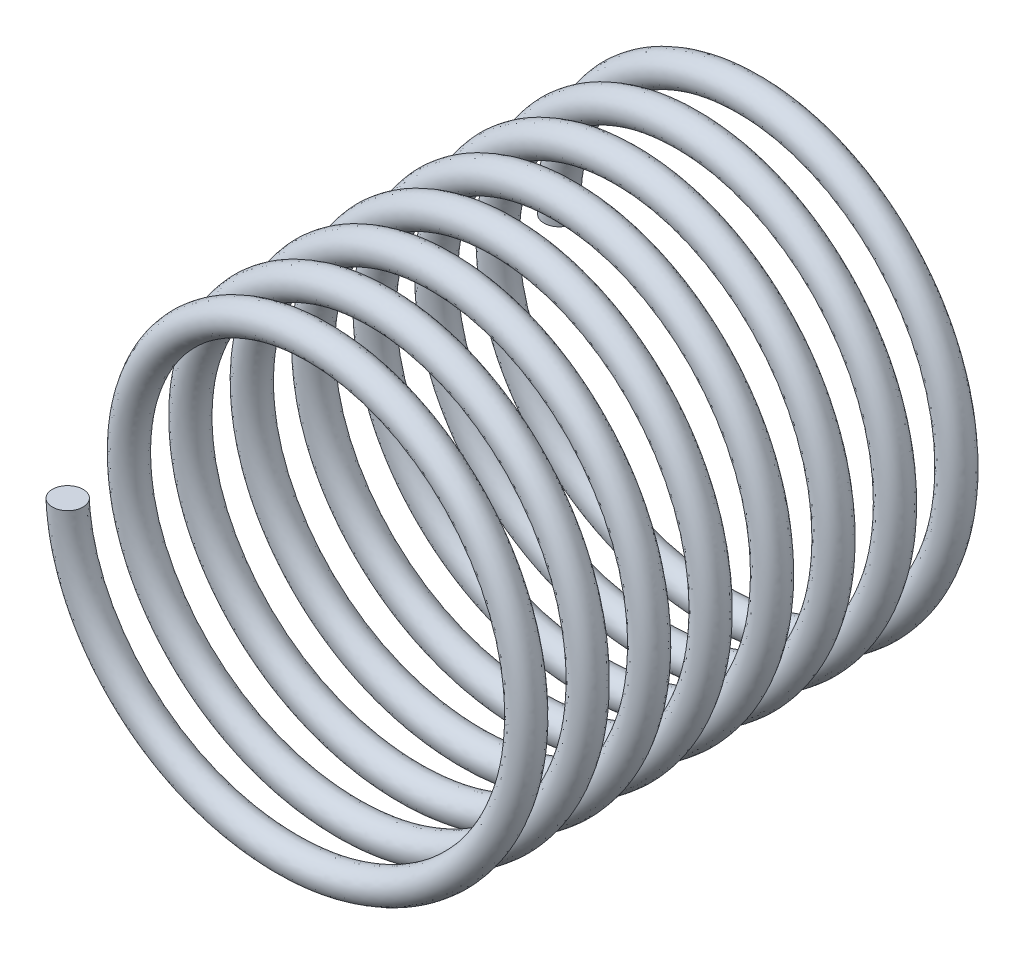
SolidWorks part; units mm, degrees
ref_plane "Front Plane" through (0, 0, 0) normal (0, 0, 1) x (1, 0, 0)
ref_plane "Top Plane" through (0, 0, 0) normal (0, 1, 0) x (1, 0, 0)
ref_plane "Right Plane" through (0, 0, 0) normal (1, 0, 0) x (0, 0, -1)
sketch "Sketch1" plane through (0, 0, 0) normal (0, 0, 1) x (1, 0, 0)
  circle A0 centre (0, 0) radius 3
  dimension "D1" = 6
curve "Helix/Spiral1" pitch 1 height 8 turns 8
sketch "Sketch2" plane through (0, 0, 0) normal (0, 1, 0) x (1, 0, 0)
  circle A0 centre (-3.4793, -7.9955) radius 0.25
  point P2 (-4.6108, -53.1692)
  point P3 (-2.4701, -26.5893)
  point P4 (-3.3708, -7.9323)
  point P5 (0, 0)
  point P6 (-3.4793, -7.9955)
sweep "Sweep1" add profiles "Sketch2" path "Helix/Spiral1"
